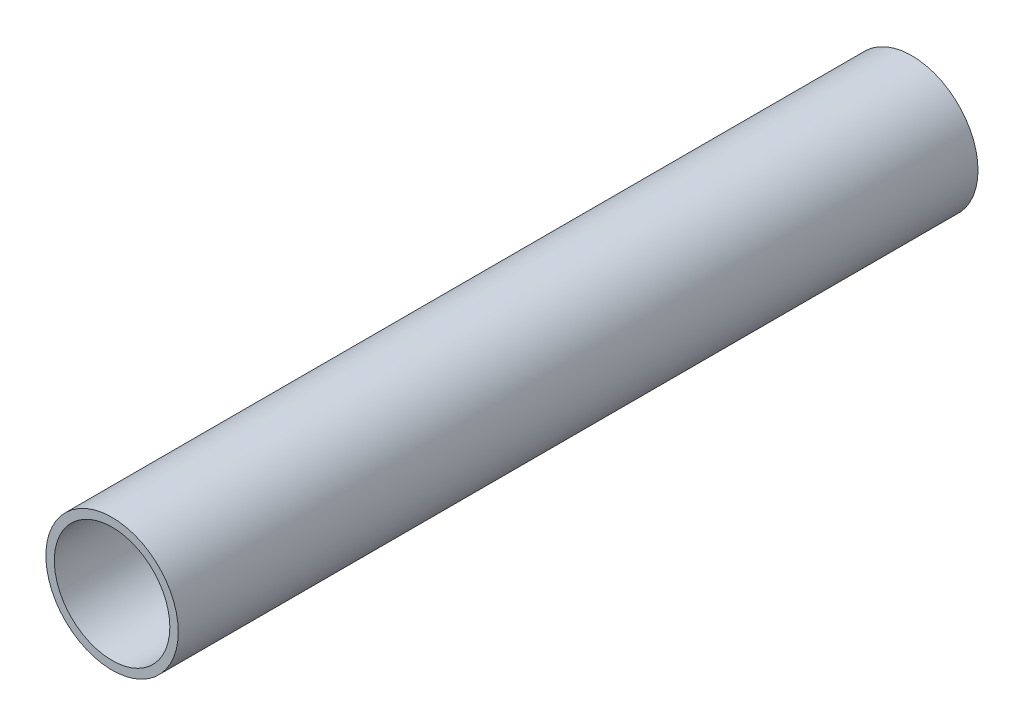
SolidWorks part; units mm, degrees
material "PVC Rigid"
ref_plane "Front Plane" through (0, 0, 0) normal (0, 0, 1) x (1, 0, 0)
ref_plane "Top Plane" through (0, 0, 0) normal (0, 1, 0) x (1, 0, 0)
ref_plane "Right Plane" through (0, 0, 0) normal (1, 0, 0) x (0, 0, -1)
sketch "Sketch1" plane through (0, 0, 0) normal (0, 0, 1) x (1, 0, 0)
  circle A0 centre (0, 0) radius 18.923
  circle A1 centre (0, 0) radius 16.51
  dimension "D1" = 37.846
  dimension "D2" = 33.02
extrude "Boss-Extrude1" add sketch "Sketch1" along normal blind 228.6
